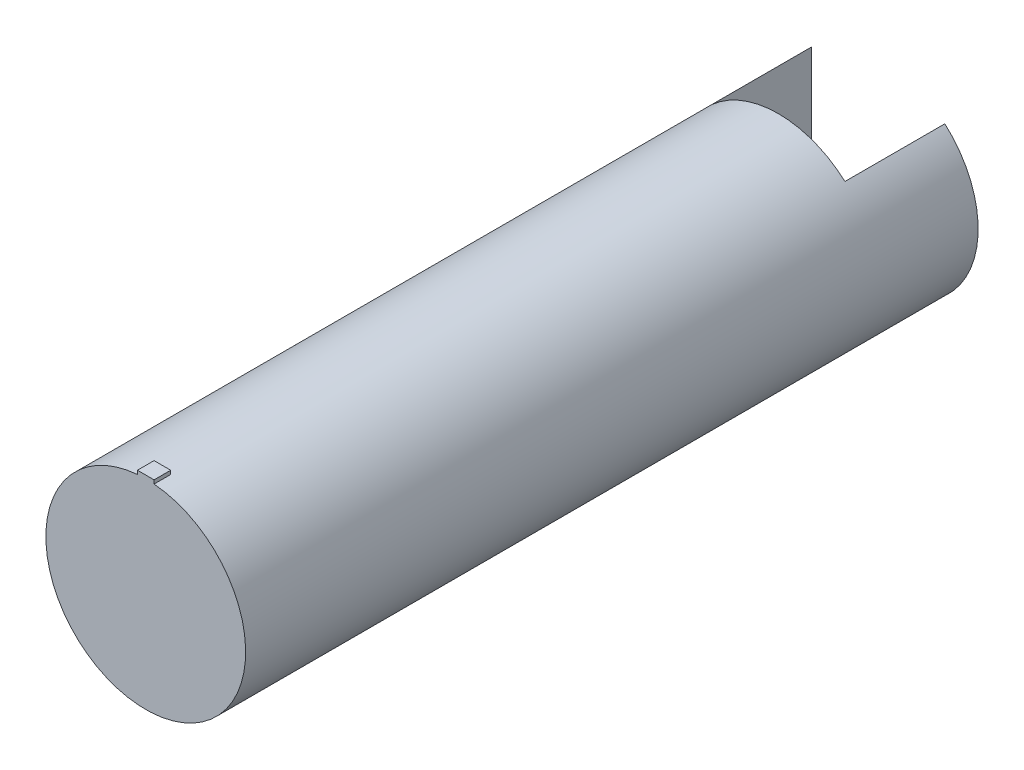
SolidWorks part; units mm, degrees
ref_plane "Front Plane" through (0, 0, 0) normal (0, 0, 1) x (1, 0, 0)
ref_plane "Top Plane" through (0, 0, 0) normal (0, 1, 0) x (1, 0, 0)
ref_plane "Right Plane" through (0, 0, 0) normal (1, 0, 0) x (0, 0, -1)
sketch "Sketch1" plane through (0, 0, 0) normal (0, 0, 1) x (1, 0, 0)
  circle A0 centre (0, 0) radius 30
  dimension "D1" = 60
extrude "Boss-Extrude1" add sketch "Sketch1" along normal blind 220
sketch "Sketch2" plane through (0, 0, 0) normal (0, 0, 1) x (1, 0, 0)
  line L1 (-20, 30) -> (20, 30)
  line L2 (-20, 30) -> (-20, -30)
  line L3 (-20, -30) -> (20, -30)
  line L4 (20, 30) -> (20, -30)
  line L5 (-20, 30) -> (20, -30) construction
  line L6 (-20, -30) -> (20, 30) construction
  point P0 (0, 0)
  dimension "D1" = 60
  dimension "D2" = 40
extrude "Cut-Extrude1" cut sketch "Sketch2" along normal blind 30
sketch "Sketch3" plane through (20, 0, 0) normal (-1, 0, 0) x (0, 0, 1)
  circle A0 centre (7.0442, 0) radius 2.5
  dimension "D1" = 5
extrude "Cut-Extrude3" cut sketch "Sketch3" against normal blind 5
ref_plane "Plane1" through (0, 0, 0) normal (-1, 0, 0) x (0, 0, 1)
mirror "Mirror1" about plane through (0, 0, 0) normal (-1, 0, 0) of "Cut-Extrude3"
sketch "Sketch4" plane through (0, 0, 0) normal (0, 1, 0) x (1, 0, 0)
  line L0 (-30, -220) -> (30, -220) construction
  line L1 (-2.5, -215) -> (2.5, -215)
  line L2 (-2.5, -215) -> (-2.5, -220)
  line L3 (-2.5, -220) -> (2.5, -220)
  line L4 (2.5, -215) -> (2.5, -220)
  line L5 (-2.5, -215) -> (2.5, -220) construction
  line L6 (-2.5, -220) -> (2.5, -215) construction
  line L8 (0, 16.5) -> (0, -16.5) construction
  point P0 (0, -217.5)
  point P9 (0.5199, -217.5)
  dimension "D1" = 5
  dimension "D2" = 5
  dimension "D3" = 0
extrude "Boss-Extrude2" add sketch "Sketch4" along normal blind 31
